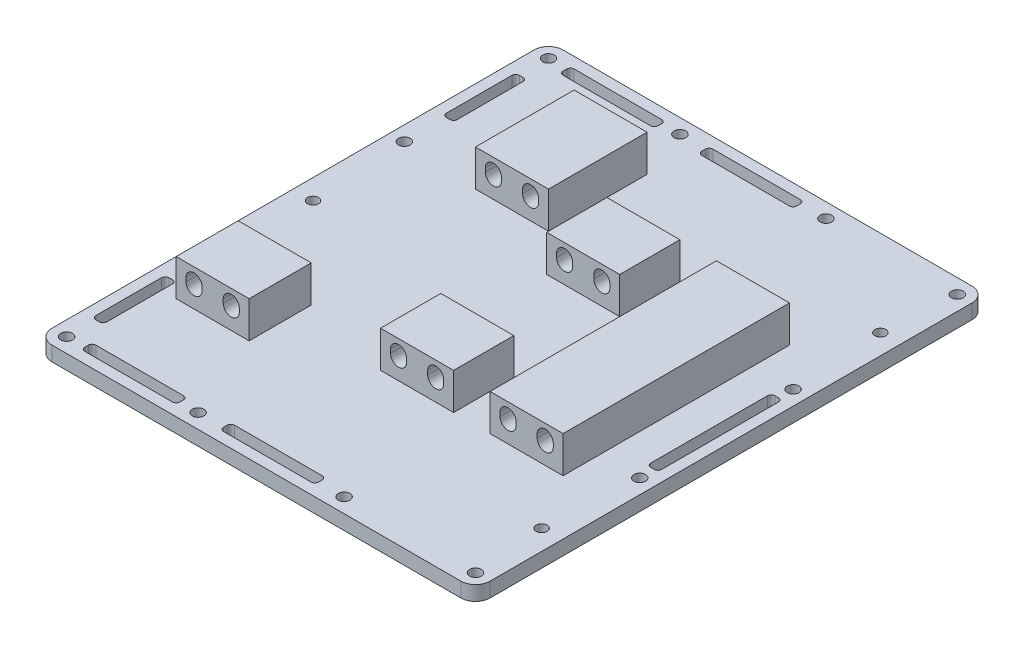
SolidWorks part; units mm, degrees
ref_plane "Front Plane" through (0, 0, 0) normal (0, 0, 1) x (1, 0, 0)
ref_plane "Top Plane" through (0, 0, 0) normal (0, 1, 0) x (1, 0, 0)
ref_plane "Right Plane" through (0, 0, 0) normal (1, 0, 0) x (0, 0, -1)
sketch "Sketch1" plane through (0, 0, 0) normal (0, 1, 0) x (1, 0, 0)
  line L1 (-60, -70) -> (60, -70)
  line L2 (-60, -70) -> (-60, 70)
  line L3 (-60, 70) -> (60, 70)
  line L4 (60, -70) -> (60, 70)
  line L5 (-60, -70) -> (60, 70) construction
  line L6 (-60, 70) -> (60, -70) construction
  point P0 (0, 0)
  dimension "D1" = 120
  dimension "D2" = 140
extrude "Boss-Extrude1" add sketch "Sketch1" along normal blind 4
sketch "Sketch2" plane through (0, 4, 0) normal (0, 1, 0) x (1, 0, 0)
  line L0 (60, 70) -> (-60, 70) construction
  line L1 (-60, 70) -> (-60, -70) construction
  line L2 (-60, -70) -> (60, -70) construction
  line L3 (60, -70) -> (60, 70) construction
  line L4 (-60, 70) -> (-60, -70) construction
  line L5 (60, -70) -> (60, 70) construction
  circle A0 centre (-56, 66) radius 1.6
  circle A1 centre (56, 66) radius 1.6
  circle A2 centre (-56, -66) radius 1.6
  circle A3 centre (56, -66) radius 1.6
  circle A6 centre (-20, -66) radius 1.6
  circle A7 centre (20, -66) radius 1.6
  circle A8 centre (-20, 66) radius 1.6
  circle A9 centre (20, 66) radius 1.6
  circle A10 centre (-56, -26.5) radius 1.6
  circle A11 centre (-56, 26.5) radius 1.6
  circle A12 centre (56, -21) radius 1.6
  circle A13 centre (56, 21) radius 1.6
  dimension "D1" = 3.2
  dimension "D6" = 3.2
  dimension "D7" = 3.2
  dimension "D12" = 3.2
  dimension "D13" = 4
  dimension "D15" = 4
  dimension "D19" = 3.2
  dimension "D20" = 3.2
  dimension "D8" = 3.2
  dimension "D23" = 3.2
  dimension "D10" = 3.2
  dimension "D16" = 3.2
  dimension "D18" = 3.2
  dimension "D28" = 3.2
  dimension "D2" = 4
  dimension "D3" = 4
  dimension "D4" = 4
  dimension "D5" = 4
  dimension "D9" = 4
  dimension "D11" = 4
  dimension "D14" = 43.5
  dimension "D17" = 43.5
  dimension "D21" = 40
  dimension "D22" = 40
  dimension "D24" = 40
  dimension "D25" = 40
  dimension "D26" = 4
  dimension "D27" = 49
  dimension "D29" = 49
  dimension "D30" = 4
extrude "Cut-Extrude1" cut sketch "Sketch2" against normal blind 4
fillet "Fillet1" radius 4 4 edges at (-60, 2, -70) (60, 2, -70) (60, 2, 70) (-60, 2, 70)
sketch "Sketch5" plane through (0, 4, 0) normal (0, 1, 0) x (1, 0, 0)
  line L0 (25, -31) -> (25, 31)
  line L1 (45, -31) -> (45, 31)
  line L6 (-15, 52) -> (-35, 52)
  line L7 (-15, 52) -> (-15, 25)
  line L8 (-15, 25) -> (-35, 25)
  line L9 (-35, 52) -> (-35, 25)
  line L10 (-5, 31) -> (15, 31)
  line L11 (-5, 31) -> (-5, -31)
  line L12 (-5, -31) -> (15, -31)
  line L13 (15, 31) -> (15, -31)
  line L14 (-50, -25) -> (-30, -25)
  line L15 (-50, -25) -> (-50, -52)
  line L16 (-50, -52) -> (-30, -52)
  line L17 (-30, -25) -> (-30, -52)
  line L18 (25, 31) -> (45, 31)
  line L19 (25, -31) -> (45, -31)
  line L20 (-60, 66) -> (-60, -66) construction
  line L21 (60, -66) -> (60, 66) construction
  line L23 (-56, -70) -> (56, -70) construction
  line L24 (56, 70) -> (-56, 70) construction
  dimension "D3" = 27
  dimension "D4" = 20
  dimension "D5" = 20
  dimension "D6" = 62
  dimension "D7" = 20
  dimension "D8" = 27
  dimension "D9" = 20
  dimension "D10" = 25
  dimension "D11" = 45
  dimension "D12" = 45
  dimension "D13" = 10
  dimension "D16" = 45
  dimension "D17" = 39
  dimension "D18" = 39
  dimension "D19" = 15
  dimension "D20" = 62
extrude "Boss-Extrude2" add sketch "Sketch5" along normal blind 10
sketch "Sketch6" plane through (0, 14, 0) normal (0, 1, 0) x (1, 0, 0)
  line L0 (-30, -52) -> (-30, -25) construction
  line L1 (-50, -52) -> (-30, -52)
  line L2 (-50, -52) -> (-50, -42)
  line L3 (-50, -42) -> (-30, -42)
  line L4 (-30, -52) -> (-30, -42)
  line L18 (-5, 31) -> (-5, -31) construction
  line L19 (-5, 14.5) -> (15, 14.5)
  line L20 (-5, 14.5) -> (-5, -14.5)
  line L21 (-5, -14.5) -> (15, -14.5)
  line L22 (15, 14.5) -> (15, -14.5)
  line L23 (15, -31) -> (15, 31) construction
  line L24 (-5, -31) -> (15, -31) construction
  line L25 (15, 31) -> (-5, 31) construction
  dimension "D1" = 16.5
  dimension "D2" = 10
  dimension "D5" = 16.5
extrude "Cut-Extrude3" cut sketch "Sketch6" against normal blind 10
sketch "Sketch7" plane through (0, 0, 31) normal (0, 0, 1) x (1, 0, 0)
  line L0 (-0.1, 9.4) -> (-0.1, 10.4) construction
  line L1 (-2.3, 9.4) -> (-2.3, 10.4)
  line L2 (2.1, 9.4) -> (2.1, 10.4)
  line L3 (-5, 14) -> (15, 14) construction
  line L4 (-5, 14) -> (-5, 4) construction
  line L5 (10.1, 9.4) -> (10.1, 10.4) construction
  line L6 (7.9, 9.4) -> (7.9, 10.4)
  line L7 (12.3, 9.4) -> (12.3, 10.4)
  line L8 (15, 14) -> (15, 4) construction
  line L9 (29.9, 9.4) -> (29.9, 10.4) construction
  line L10 (27.7, 9.4) -> (27.7, 10.4)
  line L11 (32.1, 9.4) -> (32.1, 10.4)
  line L12 (40.1, 9.4) -> (40.1, 10.4) construction
  line L13 (37.9, 9.4) -> (37.9, 10.4)
  line L14 (42.3, 9.4) -> (42.3, 10.4)
  line L15 (25, 14) -> (25, 4) construction
  line L16 (25, 14) -> (45, 14) construction
  line L17 (45, 14) -> (45, 4) construction
  line L18 (-56, 4) -> (56, 4) construction
  arc A0 (-2.3, 9.4) -> (2.1, 9.4) centre (-0.1, 9.4) ccw
  arc A1 (2.1, 10.4) -> (-2.3, 10.4) centre (-0.1, 10.4) ccw
  arc A2 (7.9, 9.4) -> (12.3, 9.4) centre (10.1, 9.4) ccw
  arc A3 (12.3, 10.4) -> (7.9, 10.4) centre (10.1, 10.4) ccw
  arc A4 (27.7, 9.4) -> (32.1, 9.4) centre (29.9, 9.4) ccw
  arc A5 (32.1, 10.4) -> (27.7, 10.4) centre (29.9, 10.4) ccw
  arc A6 (37.9, 9.4) -> (42.3, 9.4) centre (40.1, 9.4) ccw
  arc A7 (42.3, 10.4) -> (37.9, 10.4) centre (40.1, 10.4) ccw
  point P2 (-0.1, 9.9)
  point P13 (10.1, 9.9)
  point P22 (29.9, 9.9)
  point P29 (40.1, 9.9)
  dimension "D3" = 2.2
  dimension "D7" = 2.2
  dimension "D10" = 2.2
  dimension "D16" = 2.2
  dimension "D2" = 1
  dimension "D4" = 4.9
  dimension "D5" = 1
  dimension "D6" = 4.1
  dimension "D8" = 4.9
  dimension "D9" = 1
  dimension "D11" = 1
  dimension "D12" = 4.9
  dimension "D13" = 4.1
  dimension "D14" = 4.9
  dimension "D15" = 4.1
  dimension "D17" = 5.9
extrude "Cut-Extrude4" cut sketch "Sketch7" against normal through all both and the other way through all
sketch "Sketch8" plane through (0, 0, 42) normal (0, 0, 1) x (1, 0, 0)
  line L0 (-45.1, 9.4) -> (-45.1, 10.4) construction
  line L1 (-47.3, 9.4) -> (-47.3, 10.4)
  line L2 (-42.9, 9.4) -> (-42.9, 10.4)
  line L3 (-34.9, 9.4) -> (-34.9, 10.4) construction
  line L4 (-37.1, 9.4) -> (-37.1, 10.4)
  line L5 (-32.7, 9.4) -> (-32.7, 10.4)
  line L6 (-30, 14) -> (-50, 14) construction
  line L7 (-50, 4) -> (-50, 14) construction
  line L8 (-30, 4) -> (-30, 14) construction
  arc A0 (-47.3, 9.4) -> (-42.9, 9.4) centre (-45.1, 9.4) ccw
  arc A1 (-42.9, 10.4) -> (-47.3, 10.4) centre (-45.1, 10.4) ccw
  arc A2 (-37.1, 9.4) -> (-32.7, 9.4) centre (-34.9, 9.4) ccw
  arc A3 (-32.7, 10.4) -> (-37.1, 10.4) centre (-34.9, 10.4) ccw
  point P2 (-45.1, 9.9)
  point P7 (-34.9, 9.9)
  dimension "D2" = 2.2
  dimension "D5" = 2.2
  dimension "D1" = 1
  dimension "D3" = 4.1
  dimension "D4" = 4.9
  dimension "D6" = 1
  dimension "D7" = 4.1
  dimension "D8" = 4.9
extrude "Cut-Extrude5" cut sketch "Sketch8" against normal blind 20
sketch "Sketch9" plane through (0, 0, -52) normal (0, 0, -1) x (-1, 0, 0)
  line L0 (19.9, 9.4) -> (19.9, 10.4) construction
  line L1 (17.7, 9.4) -> (17.7, 10.4)
  line L2 (22.1, 9.4) -> (22.1, 10.4)
  line L3 (30.1, 9.4) -> (30.1, 10.4) construction
  line L4 (27.9, 9.4) -> (27.9, 10.4)
  line L5 (32.3, 9.4) -> (32.3, 10.4)
  line L6 (15, 14) -> (15, 4) construction
  line L7 (15, 14) -> (35, 14) construction
  line L8 (35, 14) -> (35, 4) construction
  arc A0 (17.7, 9.4) -> (22.1, 9.4) centre (19.9, 9.4) ccw
  arc A1 (22.1, 10.4) -> (17.7, 10.4) centre (19.9, 10.4) ccw
  arc A2 (27.9, 9.4) -> (32.3, 9.4) centre (30.1, 9.4) ccw
  arc A3 (32.3, 10.4) -> (27.9, 10.4) centre (30.1, 10.4) ccw
  point P2 (19.9, 9.9)
  point P7 (30.1, 9.9)
  dimension "D3" = 2.2
  dimension "D6" = 2.2
  dimension "D1" = 1
  dimension "D2" = 4.9
  dimension "D4" = 4.1
  dimension "D5" = 1
  dimension "D7" = 4.1
  dimension "D8" = 4.9
extrude "Cut-Extrude6" cut sketch "Sketch9" against normal blind 30
sketch "Sketch10" plane through (0, 4, 0) normal (0, 1, 0) x (1, 0, 0)
  line L0 (-60, 66) -> (-60, -66) construction
  line L1 (-56, 58) -> (-55, 58)
  line L2 (-57, 57) -> (-57, 39)
  line L3 (-56, 38) -> (-55, 38)
  line L4 (-54, 57) -> (-54, 39)
  line L5 (-50, 67) -> (-26, 67)
  line L6 (-51, 66) -> (-51, 65)
  line L7 (-50, 64) -> (-26, 64)
  line L8 (-25, 66) -> (-25, 65)
  line L9 (-12, 67) -> (12, 67)
  line L10 (-13, 66) -> (-13, 65)
  line L11 (-12, 64) -> (12, 64)
  line L12 (13, 66) -> (13, 65)
  line L13 (55, 17) -> (56, 17)
  line L14 (54, 16) -> (54, -16)
  line L15 (55, -17) -> (56, -17)
  line L16 (57, 16) -> (57, -16)
  line L17 (56, 70) -> (-56, 70) construction
  line L18 (60, -66) -> (60, 66) construction
  arc A0 (54, -16) -> (55, -17) centre (55, -16) ccw
  arc A1 (56, -17) -> (57, -16) centre (56, -16) ccw
  arc A2 (56, 17) -> (57, 16) centre (56, 16) cw
  arc A3 (55, 17) -> (54, 16) centre (55, 16) ccw
  arc A4 (12, 67) -> (13, 66) centre (12, 66) cw
  arc A5 (12, 64) -> (13, 65) centre (12, 65) ccw
  arc A6 (-13, 65) -> (-12, 64) centre (-12, 65) ccw
  arc A7 (-12, 67) -> (-13, 66) centre (-12, 66) ccw
  arc A8 (-26, 64) -> (-25, 65) centre (-26, 65) ccw
  arc A9 (-26, 67) -> (-25, 66) centre (-26, 66) cw
  arc A10 (-51, 65) -> (-50, 64) centre (-50, 65) ccw
  arc A11 (-50, 67) -> (-51, 66) centre (-50, 66) ccw
  arc A12 (-57, 39) -> (-56, 38) centre (-56, 39) ccw
  arc A13 (-55, 38) -> (-54, 39) centre (-55, 39) ccw
  arc A14 (-55, 58) -> (-54, 57) centre (-55, 57) cw
  arc A15 (-56, 58) -> (-57, 57) centre (-56, 57) ccw
  point P24 (54, -17)
  point P27 (57, -17)
  point P30 (57, 17)
  point P35 (13, 67)
  point P38 (13, 64)
  point P43 (-13, 67)
  point P46 (-25, 64)
  point P49 (-25, 67)
  point P54 (-51, 67)
  point P59 (-54, 38)
  point P62 (-54, 58)
  point P65 (-57, 58)
  dimension "D17" = 1
  dimension "D1" = 3
  dimension "D2" = 3
  dimension "D3" = 3
  dimension "D4" = 26
  dimension "D5" = 26
  dimension "D6" = 20
  dimension "D7" = 3
  dimension "D8" = 12
  dimension "D9" = 9
  dimension "D10" = 3
  dimension "D11" = 3
  dimension "D12" = 47
  dimension "D13" = 3
  dimension "D14" = 3
  dimension "D15" = 53
  dimension "D16" = 34
extrude "Cut-Extrude7" cut sketch "Sketch10" against normal through all
mirror "Mirror1" about plane through (0, 0, 0) normal (0, 0, 1) of "Cut-Extrude7"
sketch "Sketch11" plane through (0, 4, 0) normal (0, 1, 0) x (1, 0, 0)
  line L0 (-60, 66) -> (-60, -66) construction
  line L1 (-56, -70) -> (56, -70) construction
  line L2 (60, -66) -> (60, 66) construction
  line L3 (56, 70) -> (-56, 70) construction
  circle A0 centre (-54.5, 0) radius 1.5
  circle A1 centre (54.5, -46.4) radius 1.5
  circle A2 centre (54.5, 46.4) radius 1.5
  dimension "D1" = 3
  dimension "D4" = 3
  dimension "D7" = 3
  dimension "D2" = 5.5
  dimension "D3" = 70
  dimension "D5" = 5.5
  dimension "D6" = 23.6
  dimension "D8" = 5.5
  dimension "D9" = 23.6
extrude "Cut-Extrude8" cut sketch "Sketch11" against normal through all
